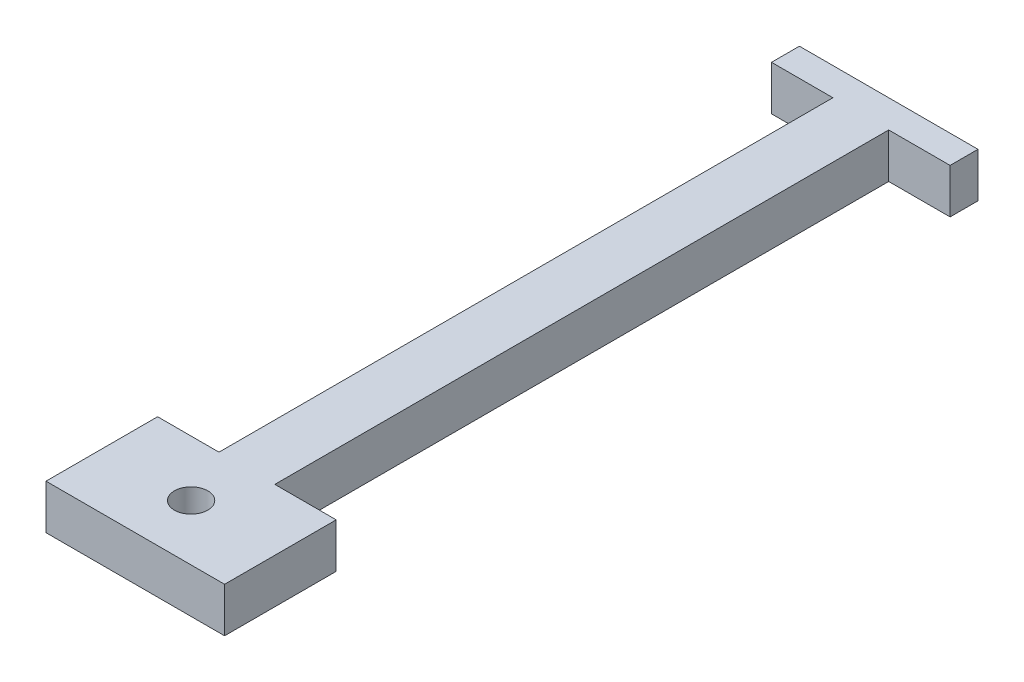
SolidWorks part; units mm, degrees
ref_plane "Front Plane" through (0, 0, 0) normal (0, 0, 1) x (1, 0, 0)
ref_plane "Top Plane" through (0, 0, 0) normal (0, 1, 0) x (1, 0, 0)
ref_plane "Right Plane" through (0, 0, 0) normal (1, 0, 0) x (0, 0, -1)
sketch "Sketch1" plane through (0, 0, 0) normal (0, 1, 0) x (1, 0, 0)
  line L0 (0, 0) -> (0, 104.3916) construction
  line L1 (8, 57.5) -> (-8, 57.5)
  line L2 (-8, 57.5) -> (-8, 55)
  line L3 (-8, 55) -> (-2.5, 55)
  line L4 (-2.5, 55) -> (-2.5, 0)
  line L5 (-2.5, 0) -> (2.5, 0)
  line L6 (2.5, 55) -> (2.5, 0)
  line L7 (8, 55) -> (2.5, 55)
  line L8 (8, 57.5) -> (8, 55)
  point P13 (0, 57.5)
  dimension "D1" = 2.5
  dimension "D2" = 8
  dimension "D3" = 2.5
  dimension "D4" = 55
extrude "Boss-Extrude1" add sketch "Sketch1" along normal blind 4
sketch "Sketch2" plane through (0, 0, 0) normal (0, 0, 1) x (1, 0, 0)
  line L0 (8, 4) -> (8, 0) construction
  line L1 (-8, 4) -> (8, 4)
  line L2 (-8, 4) -> (-8, 0)
  line L3 (-8, 0) -> (8, 0)
  line L4 (8, 4) -> (8, 0)
extrude "Boss-Extrude2" add sketch "Sketch2" along normal blind 10
sketch "Sketch3" plane through (0, 4, 0) normal (0, 1, 0) x (1, 0, 0)
  line L0 (0, 57.5) -> (0, -10) construction
  line L1 (8, 57.5) -> (-8, 57.5) construction
  line L2 (8, -10) -> (-8, -10) construction
  line L4 (-1.5, -3.5) -> (1.5, -3.5) construction
  line L5 (-1.5, -3.5) -> (-1.5, -6.5) construction
  line L6 (-1.5, -6.5) -> (1.5, -6.5) construction
  line L7 (1.5, -3.5) -> (1.5, -6.5) construction
  line L8 (-1.5, -3.5) -> (1.5, -6.5) construction
  line L9 (-1.5, -6.5) -> (1.5, -3.5) construction
  circle A0 centre (0, -5) radius 1.5
  dimension "D1" = 3
  dimension "D2" = 5
extrude "Cut-Extrude1" cut sketch "Sketch3" against normal blind 10
